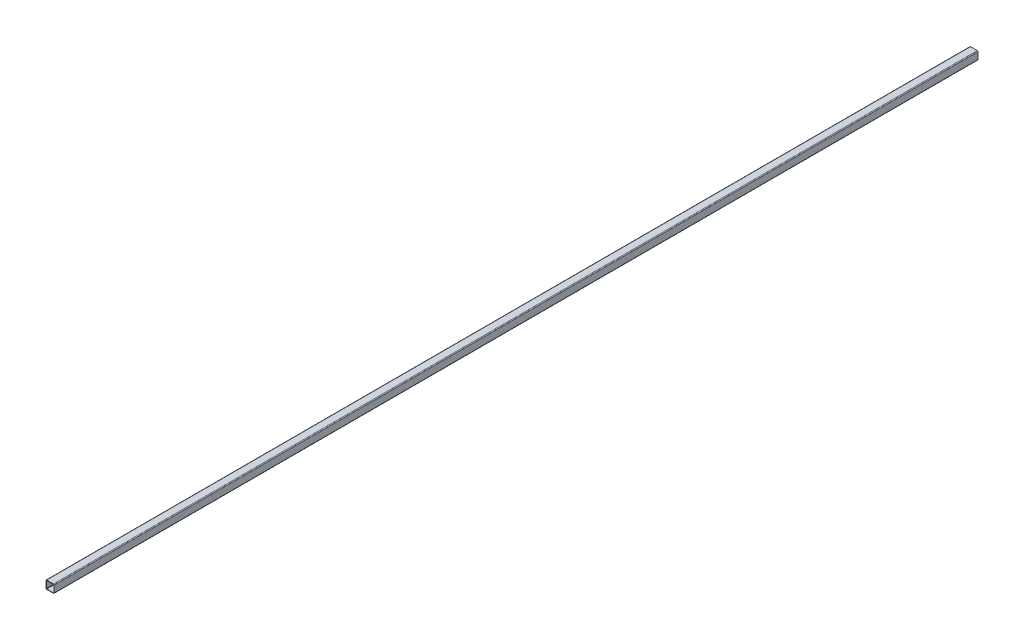
SolidWorks part; units mm, degrees
material "Thornel Mat VMA"
ref_plane "Front Plane" through (0, 0, 0) normal (0, 0, 1) x (1, 0, 0)
ref_plane "Top Plane" through (0, 0, 0) normal (0, 1, 0) x (1, 0, 0)
ref_plane "Right Plane" through (0, 0, 0) normal (1, 0, 0) x (0, 0, -1)
sketch "Sketch1" plane through (0, 0, 0) normal (0, 0, 1) x (1, 0, 0)
  line L0 (-12.5603, 11.2903) -> (-12.5603, -11.2903)
  line L1 (-11.2903, 13.8303) -> (11.2903, 13.8303)
  line L2 (-13.8303, 11.2903) -> (-13.8303, -11.2903)
  line L3 (-11.2903, -13.8303) -> (11.2903, -13.8303)
  line L4 (13.8303, 11.2903) -> (13.8303, -11.2903)
  line L5 (-11.2903, -12.5603) -> (11.2903, -12.5603)
  line L6 (12.5603, 11.2903) -> (12.5603, -11.2903)
  line L7 (-11.2903, 12.5603) -> (11.2903, 12.5603)
  arc A0 (-13.8303, -11.2903) -> (-11.2903, -13.8303) centre (-11.2903, -11.2903) ccw
  arc A1 (11.2903, -13.8303) -> (13.8303, -11.2903) centre (11.2903, -11.2903) ccw
  arc A2 (11.2903, 13.8303) -> (13.8303, 11.2903) centre (11.2903, 11.2903) cw
  arc A3 (-11.2903, 13.8303) -> (-13.8303, 11.2903) centre (-11.2903, 11.2903) ccw
  arc A4 (-12.5603, -11.2903) -> (-11.2903, -12.5603) centre (-11.2903, -11.2903) ccw
  arc A5 (11.2903, -12.5603) -> (12.5603, -11.2903) centre (11.2903, -11.2903) ccw
  arc A6 (11.2903, 12.5603) -> (12.5603, 11.2903) centre (11.2903, 11.2903) cw
  arc A7 (-11.2903, 12.5603) -> (-12.5603, 11.2903) centre (-11.2903, 11.2903) ccw
  point P4 (0, 13.8303)
  point P6 (13.8303, 0)
  point P13 (13.8303, 13.8303)
  point P16 (-13.8303, 13.8303)
  dimension "D2" = 2.54
  dimension "D1" = 27.6606
  dimension "D3" = 1.27
extrude "Boss-Extrude1" add sketch "Sketch1" along normal mid plane 3127.375
